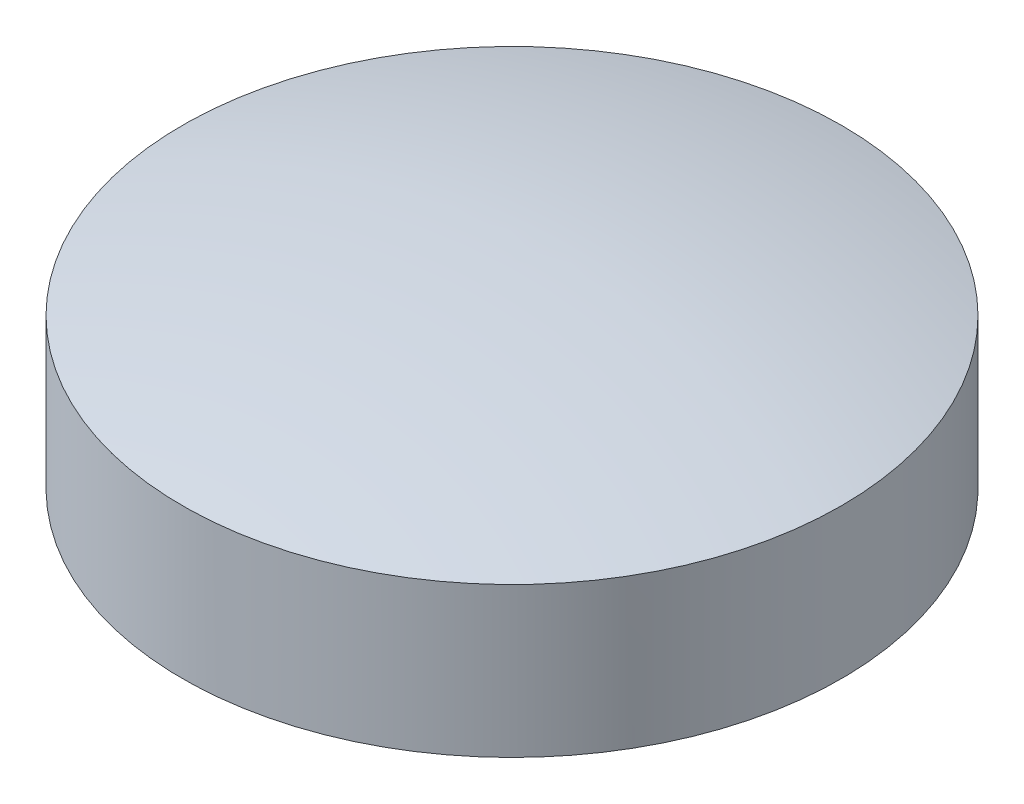
SolidWorks part; units mm, degrees
ref_plane "Front Plane" through (0, 0, 0) normal (0, 0, 1) x (1, 0, 0)
ref_plane "Top Plane" through (0, 0, 0) normal (0, 1, 0) x (1, 0, 0)
ref_plane "Right Plane" through (0, 0, 0) normal (1, 0, 0) x (0, 0, -1)
sketch "Sketch1" plane through (0, 0, 0) normal (0, 0, 1) x (1, 0, 0)
  line L0 (0, 0) -> (0, 14.6071) construction
  line L1 (0, 0) -> (22, 0)
  line L2 (22, 0) -> (22, 10)
  line L3 (0, 13) -> (0, 0)
  arc A0 (0, 13) -> (22, 10) centre (0, -69.1667) cw
  dimension "D3" = 44
  dimension "D1" = 3
  dimension "D2" = 10
revolve "Revolve1" add sketch "Sketch1" angle 360 about L0
